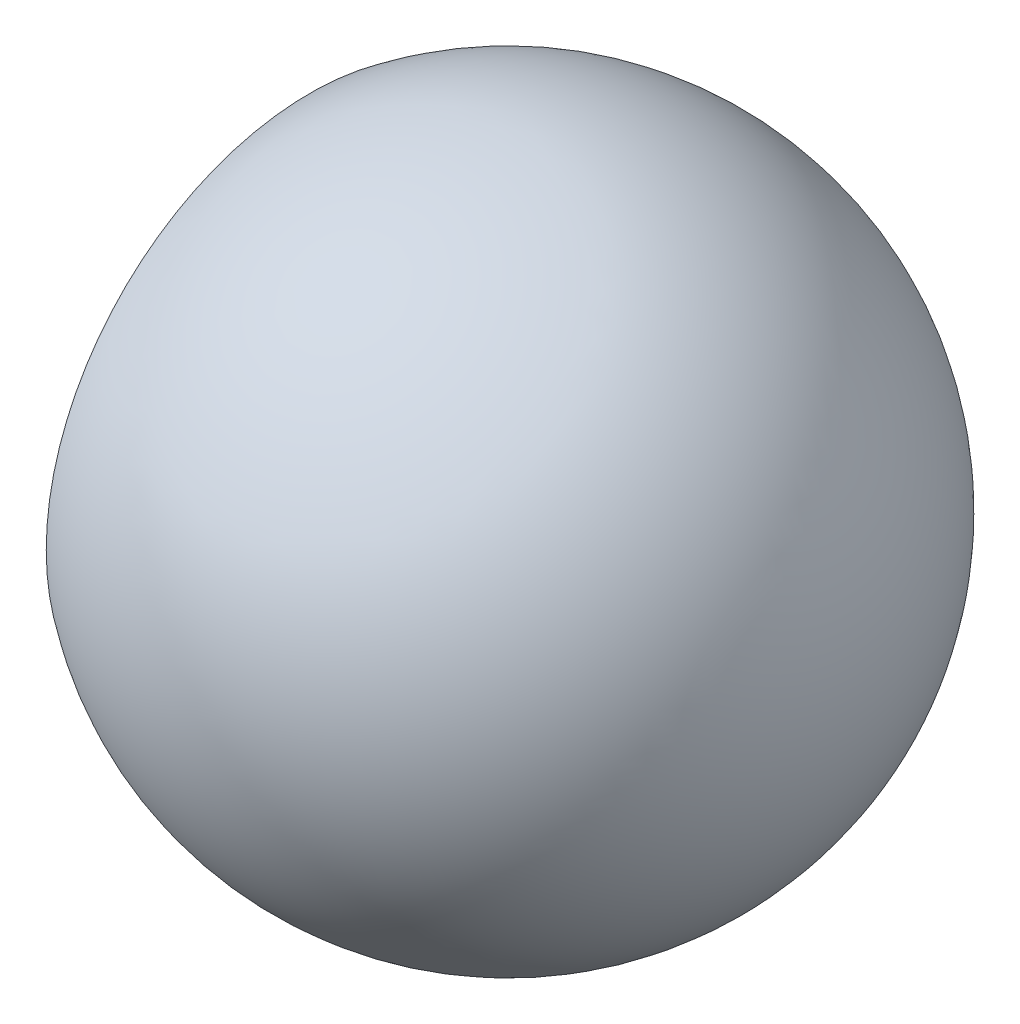
SolidWorks part; units mm, degrees
material "Резина"
ref_plane "Спереди" through (0, 0, 0) normal (0, 0, 1) x (1, 0, 0)
ref_plane "Сверху" through (0, 0, 0) normal (0, 1, 0) x (1, 0, 0)
ref_plane "Справа" through (0, 0, 0) normal (1, 0, 0) x (0, 0, -1)
sketch "Эскиз5" plane through (0, 0, 0) normal (0, 0, 1) x (1, 0, 0)
  line L0 (0, 0) -> (10, 0)
  line L2 (0, 0) -> (-6, 0)
  line L3 (-6, 0) -> (-6, -8)
  arc A0 (-6, -8) -> (10, 0) centre (0, 0) ccw
  point P1 (0.3193, -3.9872)
  point P3 (-0.0846, 0)
  dimension "D1" = 20
  dimension "D3" = 6
revolve "Повернуть2" add sketch "Эскиз5" angle 360 about L0
